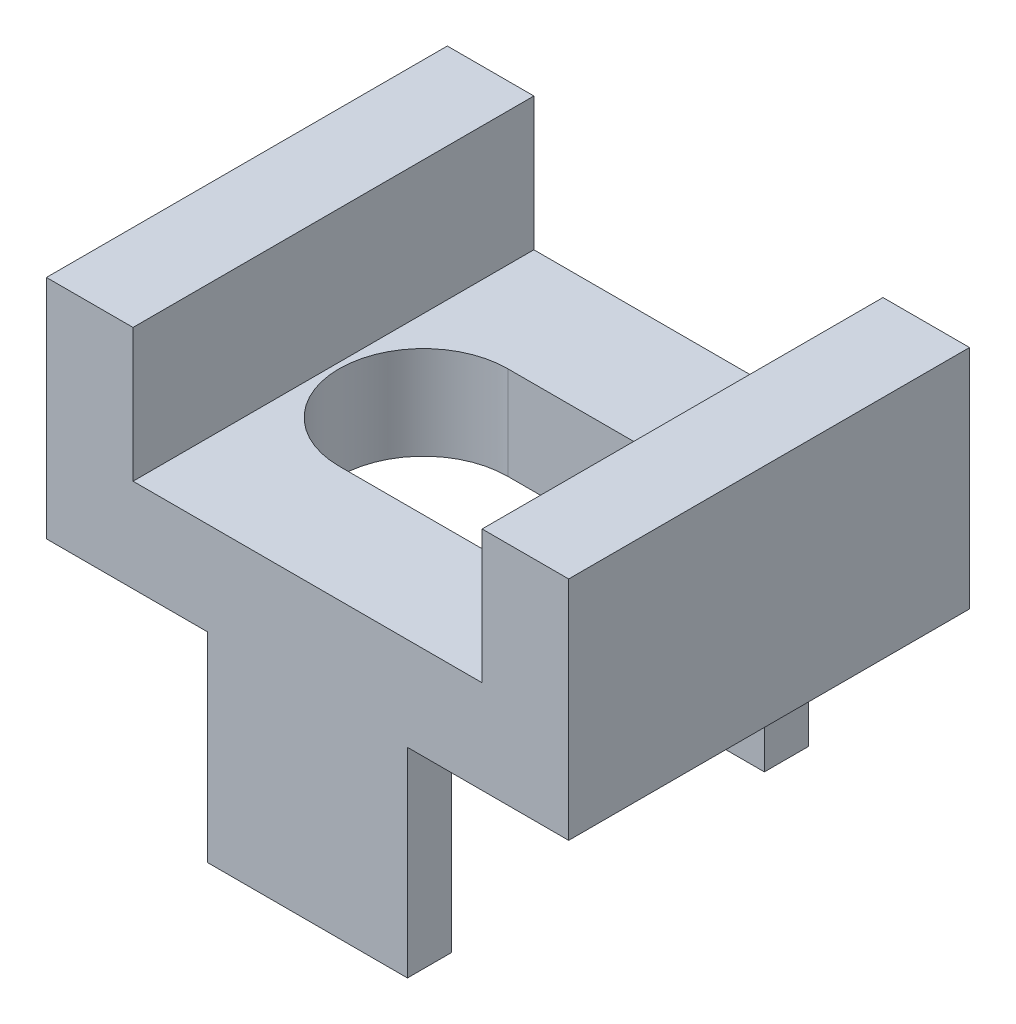
SolidWorks part; units mm, degrees
ref_plane "Front Plane" through (0, 0, 0) normal (0, 0, 1) x (1, 0, 0)
ref_plane "Top Plane" through (0, 0, 0) normal (0, 1, 0) x (1, 0, 0)
ref_plane "Right Plane" through (0, 0, 0) normal (1, 0, 0) x (0, 0, -1)
sketch "Sketch1" plane through (0, 15.2179, 0) normal (0, 1, 0) x (0, 0, 1)
  line L0 (1.7645, -28.4723) -> (1.7645, -29.7423) construction
  line L1 (0.9136, -27.6468) -> (2.6154, -27.6468) construction
  line L2 (0.2596, -31.0678) -> (3.2694, -31.0678)
  line L3 (0.2596, -31.0678) -> (0.2596, -27.1468)
  line L4 (0.2596, -27.1468) -> (3.2694, -27.1468)
  line L5 (3.2694, -31.0678) -> (3.2694, -27.1468)
  line L6 (0.2596, -31.0678) -> (3.2694, -27.1468) construction
  line L7 (0.2596, -27.1468) -> (3.2694, -31.0678) construction
  line L8 (2.8694, -27.9008) -> (2.8694, -30.3138) construction
  line L9 (1.7645, -29.7423) -> (1.7645, -28.4723) construction
  line L10 (1.1311, -29.7423) -> (1.1311, -28.4723)
  line L11 (2.3979, -29.7423) -> (2.3979, -28.4723)
  arc A0 (1.1311, -29.7423) -> (2.3979, -29.7423) centre (1.7645, -29.7423) ccw
  arc A1 (2.3979, -28.4723) -> (1.1311, -28.4723) centre (1.7645, -28.4723) ccw
  circle A3 centre (1.7645, -28.4723) radius 0.5334 construction
  point P4 (1.7645, -29.1073)
  point P14 (1.7645, -29.1073)
  dimension "D3" = 0.1
  dimension "D1" = 0.5
  dimension "D2" = 0.4
extrude "Boss-Extrude1" add sketch "Sketch1" along normal blind 0.7
sketch "Sketch2" plane through (0, 15.2179, 0) normal (0, -1, 0) x (0, 0, -1)
  line L0 (-1.7645, 1.8828) -> (-3.2694, 1.8828) construction
  line L2 (-3.2694, -31.0678) -> (-3.2694, -27.1468) construction
other "Snap Hook1" [suppressed] parameters "BaseDepth"=0.5, "TopDepth"=0.4, "Width"=1.247, "HookHeight"=0.5, "Overhang"=0.2, "BodyHeight"=5.4752, "Draft"=9, "LipHeight"=0.3
sketch "Sketch3" plane through (0, 15.2179, 0) normal (0, -1, 0) x (0, 0, -1)
  line L0 (-2.8694, -29.078) -> (-2.8694, -31.0678) construction
  line L1 (-2.8694, -29.3123) -> (-2.8694, -28.8436) construction
  line L2 (-0.2596, -31.0678) -> (-3.2694, -31.0678) construction
sketch "Sketch4" plane through (0, 15.2179, 0) normal (0, -1, 0) x (0, 0, -1)
  line L0 (-2.8694, -29.1073) -> (-3.2694, -29.1073) construction
  line L3 (-3.2694, -31.0678) -> (-3.2694, -27.1468) construction
  line L8 (-2.8694, -28.8436) -> (-2.8694, -28.697) construction
  line L9 (-2.9394, -29.1073) -> (-3.2694, -29.1073)
  line L10 (-2.9394, -29.1073) -> (-2.9394, -28.3573)
  line L11 (-2.9394, -28.3573) -> (-3.2694, -28.3573)
  line L12 (-3.2694, -29.1073) -> (-3.2694, -28.3573)
  line L13 (-2.8694, -27.9008) -> (-2.8694, -30.3138) construction
  dimension "D1" = 0.75
  dimension "D2" = 0.07
extrude "Boss-Extrude2" add sketch "Sketch4" along normal blind 1.5 contours L11 L12 L9 L10
ref_plane "Plane1" through (-39.1073, 0, 0) normal (-1, 0, 0) x (0, 1, 0)
ref_plane "Plane2" through (0, 0, 1.7645) normal (0, 0, 1) x (1, 0, 0)
mirror "Mirror8" about plane through (0, 0, 1.7645) normal (0, 0, 1) of "Boss-Extrude2"
mirror "Mirror9" about plane through (-29.1073, 13.7179, 0.5896) normal (1, 0, 0) of "Mirror8", "Boss-Extrude2"
sketch "Sketch5" plane through (0, 15.9179, 0) normal (0, 1, 0) x (0, 0, 1)
  line L0 (3.2694, -31.0678) -> (3.2694, -27.1468) construction
  line L1 (0.2596, -27.1468) -> (3.2694, -27.1468)
  line L2 (0.2596, -27.1468) -> (0.2596, -27.7968)
  line L3 (0.2596, -27.7968) -> (3.2694, -27.7968)
  line L4 (3.2694, -27.1468) -> (3.2694, -27.7968)
  dimension "D1" = 0.65
extrude "Boss-Extrude3" add sketch "Sketch5" along normal blind 1 contours L3 L4 L1 L2
ref_plane "Plane3" through (-29.1073, 0, 0) normal (1, 0, 0) x (0, -1, 0)
mirror "Mirror10" about plane through (-29.1073, 0, 0) normal (1, 0, 0) of "Boss-Extrude3"
